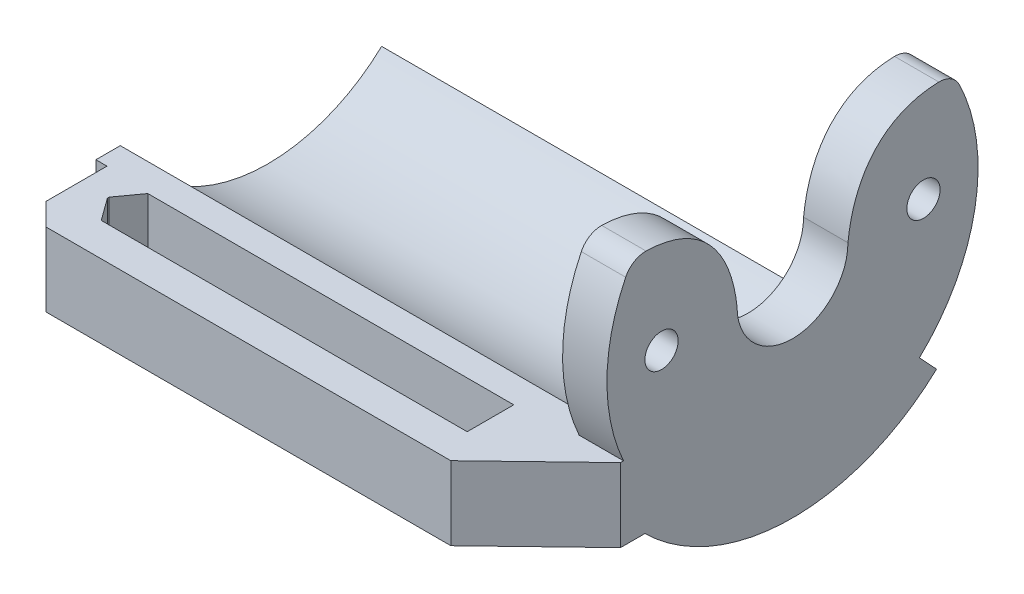
SolidWorks part; units mm, degrees
ref_plane "Front Plane" through (0, 0, 0) normal (0, 0, 1) x (1, 0, 0)
ref_plane "Top Plane" through (0, 0, 0) normal (0, 1, 0) x (1, 0, 0)
ref_plane "Right Plane" through (0, 0, 0) normal (1, 0, 0) x (0, 0, -1)
sketch "Sketch2" plane through (0, 0, 0) normal (1, 0, 0) x (0, 0, -1)
  line L2 (0, 0) -> (0, 10.7322) construction
  arc A0 (-15, 0) -> (15, 0) centre (0, 0) ccw construction
  arc A1 (-6.35, 0) -> (6.35, 0) centre (0, 0) ccw
  arc A2 (-21.25, 0) -> (21.25, 0) centre (0, 0) ccw
  arc A3 (-19.1044, 9.305) -> (-16.7651, 10.7322) centre (-16.8209, 8.1928) cw
  arc A4 (-21.25, 0) -> (-19.1044, 9.305) centre (0, 0) cw
  arc A5 (19.1044, 9.305) -> (16.7651, 10.7322) centre (16.8209, 8.1928) ccw
  arc A6 (21.25, 0) -> (19.1044, 9.305) centre (0, 0) ccw
  circle A7 centre (-15, 0) radius 1.905
  circle A8 centre (15, 0) radius 1.905
  spline S0 degree 3 poles (-16.7651, 10.7322) (-10.9952, 10.6054) (-7.0937, 6.8237) (-6.35, 0) knots 0.082135 0.082135 0.082135 0.082135 1 1 1 1
  spline S1 degree 3 poles (16.7651, 10.7322) (10.9952, 10.6054) (7.0937, 6.8237) (6.35, 0) knots 0.082135 0.082135 0.082135 0.082135 1 1 1 1
  dimension "D4" = 2.54
  dimension "D5" = 3.81
  dimension "D1" = 30
  dimension "D2" = 12.7
  dimension "D3" = 42.5
extrude "Boss-Extrude1" add sketch "Sketch2" along normal blind 5.08
sketch "Sketch3" plane through (0, 0, 0) normal (-1, 0, 0) x (0, 0, 1)
  line L0 (-13.0247, -13.9018) -> (-16.4979, -17.6089)
  line L2 (16.9031, -8.7856) -> (16.9031, -17.2204)
  line L3 (0, 0) -> (19.05, 0) construction
  arc A0 (-13.0247, -13.9018) -> (16.9031, -8.7856) centre (0, 0) ccw
  arc A5 (-16.4979, -17.6089) -> (21.4106, -11.1285) centre (0, 0) ccw
  arc M8 (-19.1044, 9.305) -> (19.1044, 9.305) centre (0, 0) ccw
  dimension "D1" = 19.05
  dimension "D3" = 19.05
  dimension "D2" = 5.08
extrude "Boss-Extrude2" add sketch "Sketch3" along normal blind 55 and the other way up to surface (5.08 mm away) contours L0 A5 L2 M8 | A0 L0 L2 M8 other way up to face at (5.08, 0, 13.095)
sketch "Sketch4" plane through (0, 0, 0) normal (-1, 0, 0) x (0, 0, 1)
  circle A0 centre (0, 0) radius 19.05
  dimension "D1" = 38.1
sketch "Sketch6" plane through (0, 0, 16.9031) normal (0, 0, 1) x (1, 0, 0)
  line L1 (-55, -8.7856) -> (5.08, -8.7856)
  line L2 (-55, -8.7856) -> (-55, -17.2204)
  line L3 (-55, -17.2204) -> (5.08, -17.2204)
  line L4 (5.08, -8.7856) -> (5.08, -17.2204)
extrude "Boss-Extrude3" add sketch "Sketch6" along normal blind 2.794
sketch "Sketch7" plane through (0, -8.7856, 0) normal (0, 1, 0) x (1, 0, 0)
  line L0 (-52.483, -20.0781) -> (-52.483, -29.2221)
  line L1 (-48.673, -20.0781) -> (-6.763, -20.0781)
  line L2 (-48.673, -20.0781) -> (-48.673, -25.4121)
  line L3 (-48.673, -25.4121) -> (-6.763, -25.4121)
  line L4 (-6.763, -20.0781) -> (-6.763, -25.4121)
  line L5 (-52.483, -29.2221) -> (-2.953, -29.2221)
  line L6 (-2.953, -20.0781) -> (-2.953, -29.2221)
  line L7 (-52.483, -20.0781) -> (-52.483, -19.6971)
  line L8 (5.08, -19.6971) -> (-55, -19.6971) construction
  line L9 (-52.483, -19.6971) -> (-2.953, -19.6971)
  line L10 (-2.953, -19.6971) -> (-2.953, -20.0781)
  line L11 (5.08, -19.6971) -> (-4.8296, -29.2221)
  line L12 (-2.953, -19.6971) -> (5.08, -19.6971)
  line L14 (-48.673, -20.0781) -> (-50.5342, -22.6457)
  line L15 (-50.5342, -22.6457) -> (-50.5342, -22.8445)
  line L16 (-50.5342, -22.8445) -> (-48.673, -25.4121)
  line L17 (-50.5342, -22.7451) -> (-48.673, -22.7451) construction
  line L18 (-53.7288, -19.6971) -> (-53.7288, -29.2221)
  line L19 (-53.7288, -29.2221) -> (-52.483, -29.2221)
  line L20 (-53.7288, -19.6971) -> (-52.483, -19.6971)
  dimension "D1" = 41.91
  dimension "D2" = 5.334
  dimension "D4" = 0.381
  dimension "D3" = 3.81
extrude "Boss-Extrude4" add sketch "Sketch7" against normal up to surface (8.4348 mm away)
chamfer "Chamfer1" distance 2.54 angle 45 1 edges at (-53.7288, -13.003, 29.2221)
